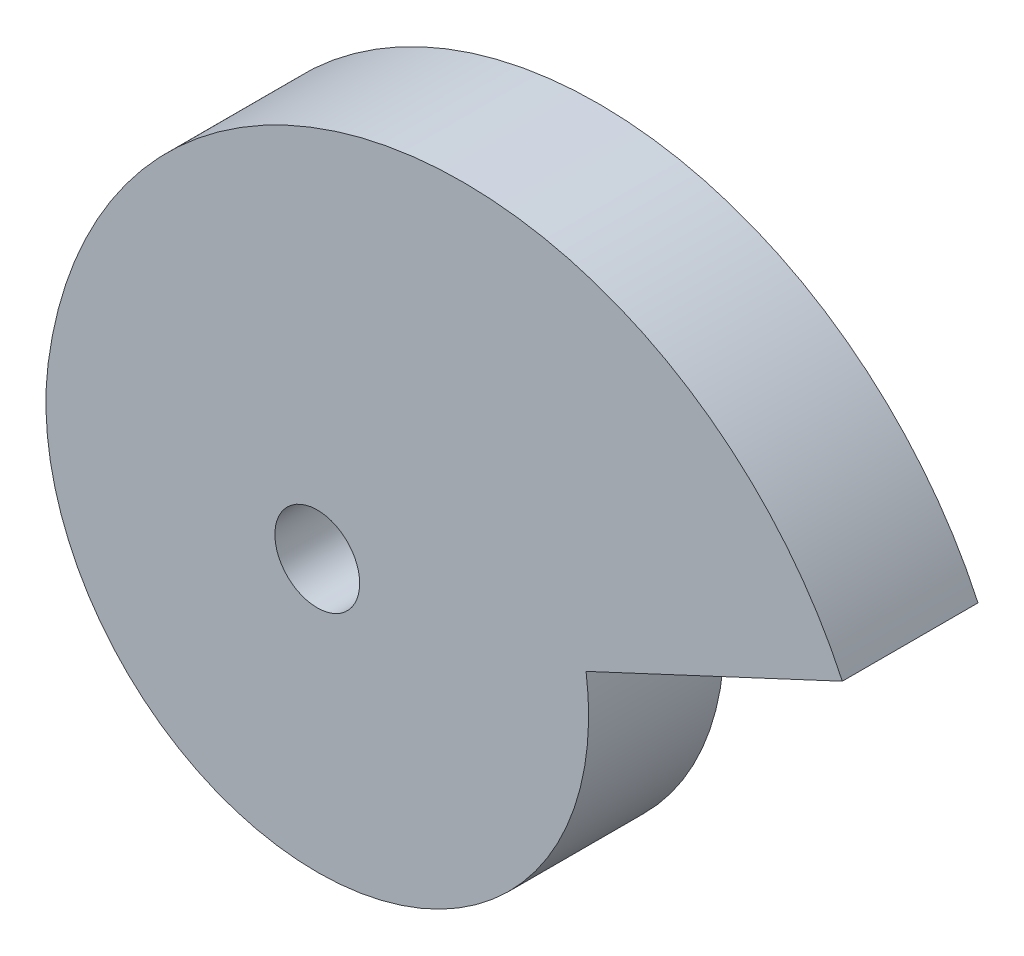
SolidWorks part; units mm, degrees
ref_plane "Front Plane" through (0, 0, 0) normal (0, 0, 1) x (1, 0, 0)
ref_plane "Top Plane" through (0, 0, 0) normal (0, 1, 0) x (1, 0, 0)
ref_plane "Right Plane" through (0, 0, 0) normal (1, 0, 0) x (0, 0, -1)
sketch "Sketch1" plane through (0, 0, 0) normal (0, 0, 1) x (1, 0, 0)
  line L1 (154.7899, 46.1567) -> (79.2529, 10.908)
  arc A0 (-79.3368, 10.2799) -> (79.2529, 10.908) centre (0, 0) ccw
  arc A2 (-79.3368, 10.2799) -> (154.7899, 46.1567) centre (42.9025, -5.559) cw
  dimension "D2" = 80
sketch "Sketch2" plane through (0, 0, 0) normal (0, 0, 1) x (1, 0, 0)
  circle A0 centre (0, 0) radius 12.5
extrude "Boss-Extrude1" add sketch "Sketch1" along normal blind 40
sketch "Sketch3" plane through (0, 0, 40) normal (0, 0, 1) x (1, 0, 0)
  circle A0 centre (0, 0) radius 12.5
extrude "Cut-Extrude1" cut sketch "Sketch3" against normal blind 40
